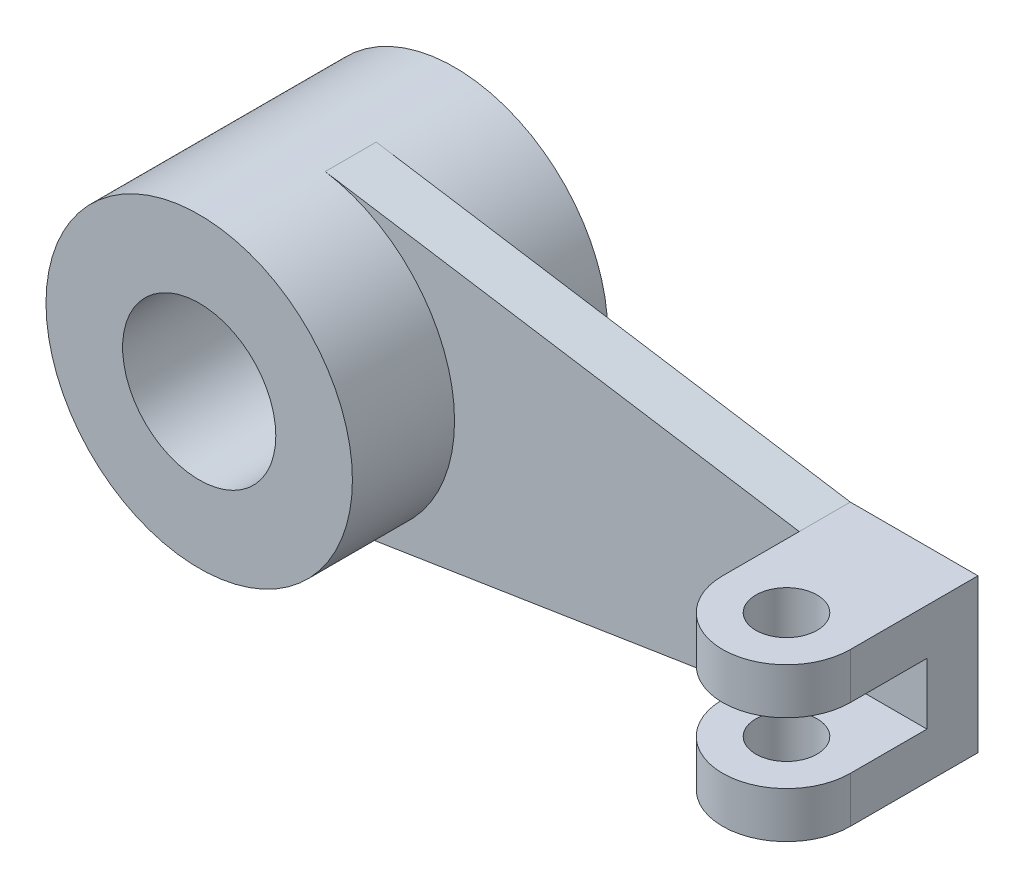
SolidWorks part; units mm, degrees
ref_plane "Front Plane" through (0, 0, 0) normal (0, 0, 1) x (1, 0, 0)
ref_plane "Top Plane" through (0, 0, 0) normal (0, 1, 0) x (1, 0, 0)
ref_plane "Right Plane" through (0, 0, 0) normal (1, 0, 0) x (0, 0, -1)
sketch "Sketch1" plane through (0, 0, 0) normal (0, 0, 1) x (1, 0, 0)
  circle A0 centre (0, 0) radius 300
  circle A1 centre (0, 0) radius 150
  dimension "D1" = 300
  dimension "D2" = 600
extrude "Boss-Extrude1" add sketch "Sketch1" along normal mid plane 500
sketch "Sketch2" plane through (0, 0, 0) normal (0, 0, 1) x (1, 0, 0)
  line L0 (46.7169, 296.3402) -> (975, 150)
  line L1 (975, 150) -> (1225, 150)
  line L2 (1225, 150) -> (1225, -150)
  line L3 (-2144.3162, 0) -> (1128.9528, 0) construction
  line L4 (975, -150) -> (1225, -150)
  line L5 (46.7169, -296.3402) -> (975, -150)
  circle A0 centre (0, 0) radius 300 construction
  arc A1 (46.7169, -296.3402) -> (46.7169, 296.3402) centre (0, 0) ccw
  point P11 (-507.6817, 0)
  point P12 (1225, 0)
  dimension "D1" = 300
  dimension "D2" = 250
  dimension "D3" = 1225
extrude "Boss-Extrude2" add sketch "Sketch2" along normal mid plane 100
sketch "Sketch3" plane through (0, -150, 0) normal (0, -1, 0) x (1, 0, 0)
  line L0 (975, 50) -> (975, 200)
  line L2 (1225, 200) -> (1225, 50)
  line L3 (975, 50) -> (1225, 50) construction
  line L4 (975, 50) -> (1225, 50)
  arc A0 (1225, 200) -> (975, 200) centre (1100, 200) ccw
  circle A1 centre (1100, 200) radius 60
  dimension "D1" = 250
  dimension "D2" = 120
extrude "Boss-Extrude3" add sketch "Sketch3" against normal blind 90
sketch "Sketch4" plane through (0, 150, 0) normal (0, 1, 0) x (1, 0, 0)
  line L0 (975, -200) -> (975, -50) construction
  line L1 (1225, -50) -> (1225, -200) construction
  line L2 (975, -50) -> (1225, -50) construction
  line L3 (975, -200) -> (975, -50)
  line L4 (1225, 50) -> (975, 50)
  line L5 (975, 50) -> (975, -50)
  line L6 (975, -50) -> (1225, -50)
  line L7 (1225, -50) -> (1225, 50)
  line L8 (1225, 50) -> (975, 50)
  line L9 (975, 50) -> (975, -50)
  line L10 (975, -50) -> (1225, -50)
  line L11 (1225, -50) -> (1225, 50)
  line L12 (1225, -50) -> (1225, -200)
  line L13 (975, -50) -> (1225, -50)
  arc A0 (975, -200) -> (1225, -200) centre (1100, -200) ccw construction
  circle A1 centre (1100, -200) radius 60 construction
  arc A2 (975, -200) -> (1225, -200) centre (1100, -200) ccw
  circle A3 centre (1100, -200) radius 60
  dimension "D1" = 0
extrude "Boss-Extrude4" add sketch "Sketch4" against normal blind 90 contours A3 | L10 L12 A2 L3
